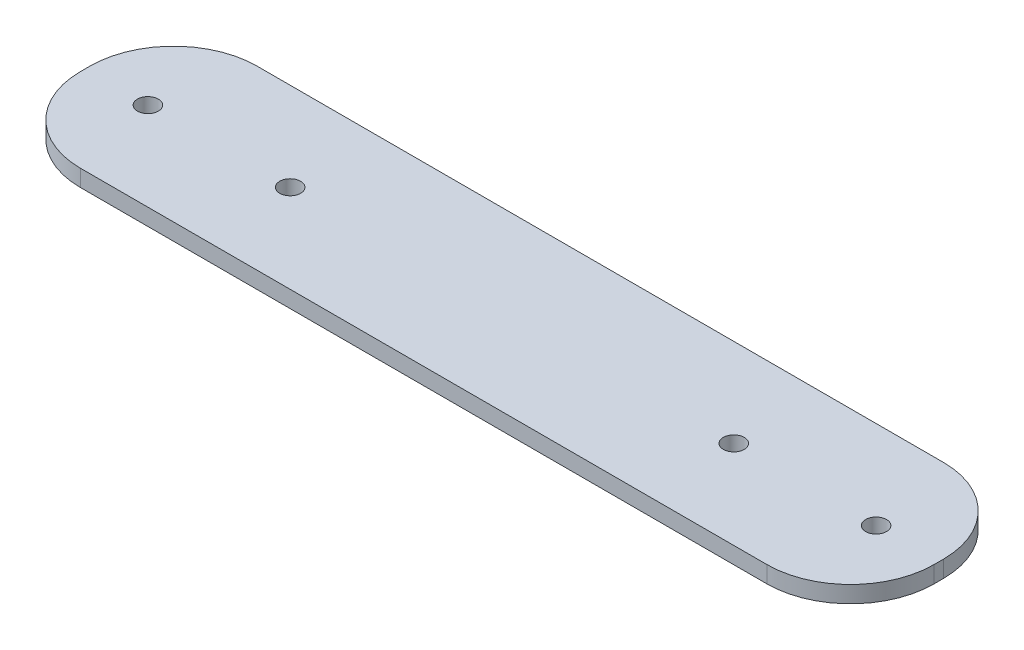
SolidWorks part; units mm, degrees
ref_plane "Front Plane" through (0, 0, 0) normal (0, 0, 1) x (1, 0, 0)
ref_plane "Top Plane" through (0, 0, 0) normal (0, 1, 0) x (1, 0, 0)
ref_plane "Right Plane" through (0, 0, 0) normal (1, 0, 0) x (0, 0, -1)
sketch "Sketch1" plane through (0, 0, 0) normal (0, 1, 0) x (1, 0, 0)
  line L0 (-62, 0) -> (62, 0) construction
  line L1 (-51, 10.5584) -> (51, 10.5584)
  line L2 (-51, 10.5584) -> (-51, -10.5584)
  line L3 (-51, -10.5584) -> (51, -10.5584)
  line L4 (51, 10.5584) -> (51, -10.5584)
  circle A0 centre (-62, 0) radius 5 construction
  circle A1 centre (62, 0) radius 5 construction
  circle A2 centre (43.5, 0) radius 1.25
  circle A3 centre (26.5, 0) radius 1.25
  circle A4 centre (-26.5, 0) radius 1.25
  circle A5 centre (-43.5, 0) radius 1.25
  point P4 (0, 10.5584)
  point P6 (-51, 0)
  point P9 (0, 0)
  dimension "D3" = 10
  dimension "D4" = 2.5
  dimension "D1" = 102
  dimension "D2" = 124
extrude "Boss-Extrude1" add sketch "Sketch1" along normal blind 2
fillet "Fillet1" radius 10 4 edges at (51, 1, -10.5584) (51, 1, 10.5584) (-51, 1, -10.5584) (-51, 1, 10.5584)
